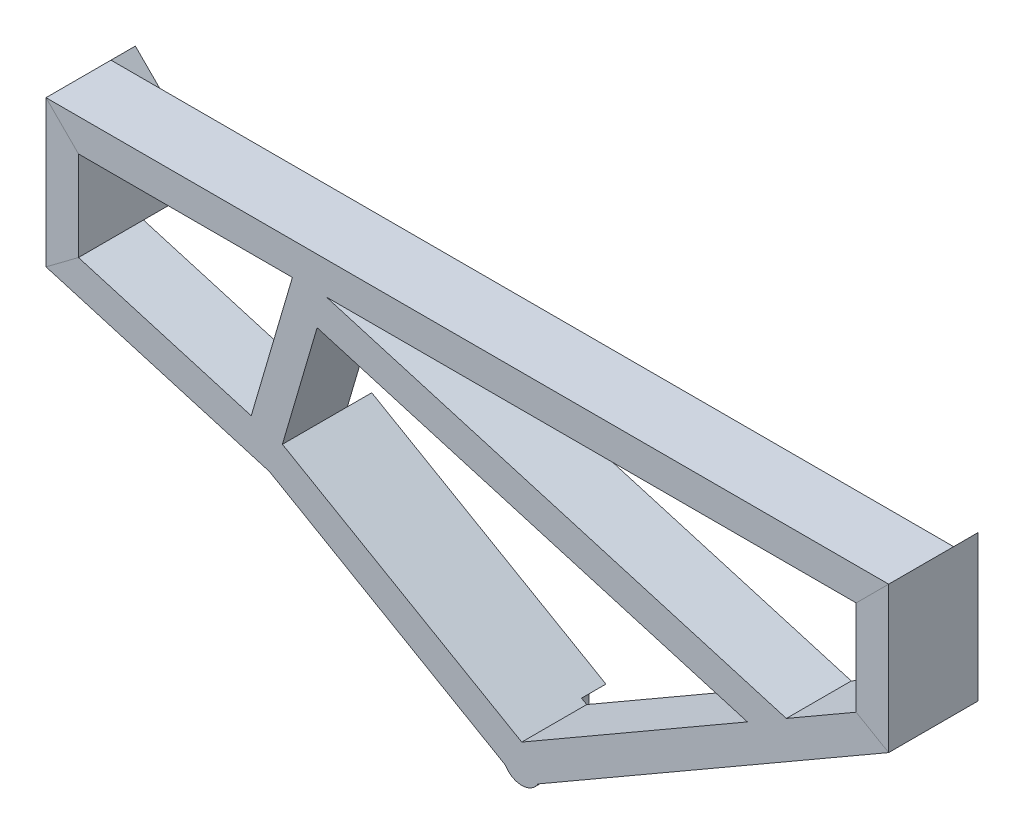
SolidWorks part; units mm, degrees
ref_plane "Спереди" through (0, 0, 0) normal (0, 0, 1) x (1, 0, 0)
ref_plane "Сверху" through (0, 0, 0) normal (0, 1, 0) x (1, 0, 0)
ref_plane "Справа" through (0, 0, 0) normal (1, 0, 0) x (0, 0, -1)
sketch "Эскиз6" plane through (0, 0, 0) normal (1, 0, 0) x (0, 0, -1)
  line L1 (-38.5518, -19.2165) -> (37.4482, -19.2165)
  line L2 (-38.5518, -19.2165) -> (-38.5518, 16.7835)
  line L3 (-38.5518, 16.7835) -> (37.4482, 16.7835)
  line L4 (37.4482, -19.2165) -> (37.4482, 16.7835)
  line L5 (-40.5518, 18.7835) -> (39.4482, 18.7835)
  line L6 (-40.5518, 18.7835) -> (-40.5518, -21.2165)
  line L7 (-40.5518, -21.2165) -> (39.4482, -21.2165)
  line L8 (39.4482, 18.7835) -> (39.4482, -21.2165)
  dimension "D1" = 36
  dimension "D2" = 76
  dimension "D3" = 2
  dimension "D4" = 2
  dimension "D5" = 2
  dimension "D6" = 2
sketch3d "Трехмерный эскиз5"
  line L0 (0, 0, 0) -> (1000, 0, 0)
  line L1 (1000, 0, 0) -> (1000, -150, 0)
  line L2 (1000, -150, 0) -> (566.9873, -400, 0)
  line L3 (566.9873, -400, 0) -> (263.8784, -225, 0)
  line L4 (263.8784, -225, 0) -> (0, -147.5843, 0)
  line L5 (0, -147.5843, 0) -> (0, 0, 0)
  line L6 (263.8784, -225, 0) -> (393.7822, 0, 0)
  line L7 (393.7822, 0, 0) -> (826.7949, -250, 0)
  dimension "D1" = 1000
  dimension "D2" = 150
  dimension "D4" = 400
  dimension "D5" = 225
  dimension "D6" = 350
  dimension "D7" = 275
  dimension "D8" = 500
sweep "По траектории13" add profiles "Эскиз6" path "Трехмерный эскиз5"
sketch "Эскиз14" plane through (-33.8938, -115.53, 0) normal (0.2815, 0.9596, 0) x (0.9596, -0.2815, 0)
  line L0 (319.0859, 39.4482) -> (57.433, 39.4482) construction
  line L1 (319.0859, -40.5518) -> (279.0859, -40.5518)
  line L2 (319.0859, -40.5518) -> (319.0859, 39.4482)
  line L3 (319.0859, 39.4482) -> (279.0859, 39.4482)
  line L4 (279.0859, -40.5518) -> (279.0859, 39.4482)
  point P7 (279.0859, -0.5518)
  dimension "D1" = 40
extrude "Бобышка-Вытянуть1" add sketch "Эскиз14" along normal blind 194
sketch "Эскиз15" plane through (306.1814, -89.8264, 0) normal (0.9596, -0.2815, 0) x (0, 0, -1)
  line L0 (-40.5518, 71.5015) -> (-40.5518, -120.3992) construction
  line L1 (-40.5518, 71.5014) -> (39.4482, 71.5014)
  line L2 (-40.5518, 71.5014) -> (-40.5518, 31.5014)
  line L3 (-40.5518, 31.5014) -> (39.4482, 31.5014)
  line L4 (39.4482, 71.5014) -> (39.4482, 31.5014)
  line L5 (39.4482, 71.5015) -> (39.4482, -120.3992) construction
  line L6 (-40.5518, 71.5015) -> (39.4482, 71.5015) construction
  dimension "D1" = 40
  dimension "D2" = 0.0001
extrude "Бобышка-Вытянуть2" add sketch "Эскиз15" along normal blind 595
sketch "Эскиз16" plane through (0, 0, -39.4482) normal (0, 0, -1) x (-1, 0, 0)
  line L0 (18.7835, 18.7835) -> (18.7835, -161.6489)
  line L1 (18.7835, -161.6489) -> (-21.2165, -131.698)
  line L2 (-21.2165, -131.698) -> (-21.2165, -21.2165)
  line L3 (-21.2165, -21.2165) -> (18.7835, 18.7835)
  line L4 (-272.2876, -205.3564) -> (-256.4335, -242.391)
  line L5 (-256.4335, -242.391) -> (-566.9873, -421.6893)
  line L6 (-566.9873, -421.6893) -> (-566.9873, -375.5013)
  line L7 (-566.9873, -375.5013) -> (-272.2876, -205.3564)
  line L8 (-1018.7835, 18.7835) -> (-978.7835, -21.2165)
  line L9 (-978.7835, -21.2165) -> (-978.7835, -137.7506)
  line L10 (-978.7835, -137.7506) -> (-1018.7835, -160.8447)
  line L11 (-1018.7835, -160.8447) -> (-1018.7835, 18.7835)
extrude "Бобышка-Вытянуть3" add sketch "Эскиз16" along normal blind 30
sketch "Эскиз17" plane through (0, 0, -69.4482) normal (0, 0, -1) x (-1, 0, 0)
  line L0 (-566.9873, -421.6893) -> (-566.9873, -375.5013) construction
  circle A0 centre (-566.9873, -398.5953) radius 23.094
  dimension "D1" = 46.188
extrude "Бобышка-Вытянуть4" add sketch "Эскиз17" against normal blind 110
sketch "Эскиз18" plane through (0, 0, -69.4482) normal (0, 0, -1) x (-1, 0, 0)
  circle A0 centre (-566.9873, -398.5953) radius 23.094
  circle A1 centre (-566.9873, -398.5953) radius 27.5
  dimension "D1" = 46.188
  dimension "D2" = 55
extrude "Вырез-Вытянуть1" cut sketch "Эскиз18" against normal blind 30
sketch "Эскиз22" plane through (0, 0, -69.4482) normal (0, 0, -1) x (-1, 0, 0)
  circle A0 centre (-566.9873, -398.5953) radius 23.094
extrude "Вырез-Вытянуть3" cut sketch "Эскиз22" against normal blind 30
sketch "Эскиз23" plane through (0, 0, -39.4482) normal (0, 0, -1) x (-1, 0, 0)
  line L0 (-566.9873, -375.5013) -> (-566.9873, -421.6893)
  arc A0 (-586.9873, -410.1423) -> (-546.9873, -410.1423) centre (-566.9873, -398.5953) ccw construction
  circle A1 centre (-566.9873, -398.5953) radius 17.5
  dimension "D1" = 35
extrude "Вырез-Вытянуть4" cut sketch "Эскиз23" against normal blind 10 contours L0 A1 | L0 A1
fillet "Скругление1" radius 0.5 1 edges at (549.4873, -398.5953, -39.4482)
